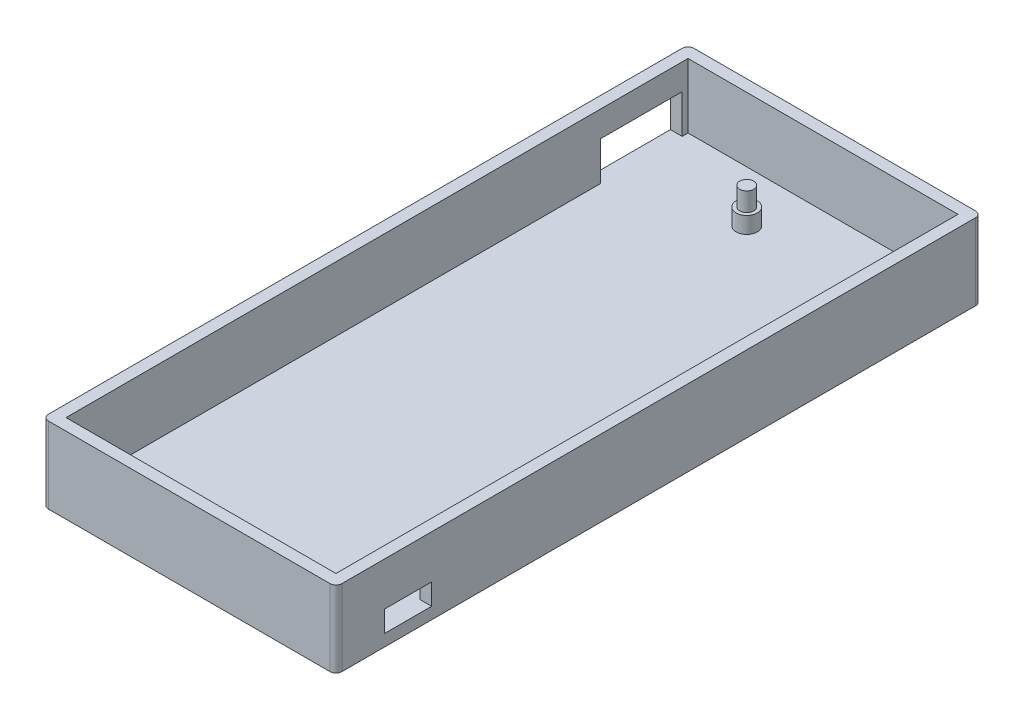
SolidWorks part; units mm, degrees
ref_plane "Front Plane" through (0, 0, 0) normal (0, 0, 1) x (1, 0, 0)
ref_plane "Top Plane" through (0, 0, 0) normal (0, 1, 0) x (1, 0, 0)
ref_plane "Right Plane" through (0, 0, 0) normal (1, 0, 0) x (0, 0, -1)
sketch "Sketch1" plane through (0, 0, 0) normal (0, 1, 0) x (1, 0, 0)
  line L1 (-77.0226, 53.0801) -> (-27.0226, 53.0801)
  line L2 (-77.0226, 53.0801) -> (-77.0226, -56.9199)
  line L3 (-77.0226, -56.9199) -> (-27.0226, -56.9199)
  line L4 (-27.0226, 53.0801) -> (-27.0226, -56.9199)
  dimension "D1" = 110
  dimension "D2" = 50
extrude "Boss-Extrude1" add sketch "Sketch1" along normal blind 2
sketch "Sketch2" plane through (0, 2, 0) normal (0, 1, 0) x (1, 0, 0)
  line L0 (-75.0226, 51.0801) -> (-75.0226, -54.9199)
  line L1 (-77.0226, 53.0801) -> (-27.0226, 53.0801)
  line L2 (-77.0226, 53.0801) -> (-77.0226, -56.9199)
  line L3 (-77.0226, -56.9199) -> (-27.0226, -56.9199)
  line L4 (-27.0226, 53.0801) -> (-27.0226, -56.9199)
  line L5 (-75.0226, -54.9199) -> (-29.0226, -54.9199)
  line L6 (-29.0226, 51.0801) -> (-29.0226, -54.9199)
  line L7 (-75.0226, 51.0801) -> (-29.0226, 51.0801)
  dimension "D1" = 2
extrude "Boss-Extrude3" add sketch "Sketch2" along normal blind 11
sketch "Sketch3" plane through (0, 2, 0) normal (0, 1, 0) x (1, 0, 0)
  circle A0 centre (-31.0226, 42.3801) radius 1.2
  circle A1 centre (-31.0226, -52.9199) radius 1.2
  circle A2 centre (-56.3226, 42.3801) radius 1.2
  circle A3 centre (-56.3226, -52.9199) radius 1.2
extrude "Boss-Extrude4" add sketch "Sketch3" along normal blind 11
sketch "Sketch4" plane through (0, 13, 0) normal (0, 1, 0) x (1, 0, 0)
  line L8 (-26.0226, 54.0801) -> (-78.0226, 54.0801)
  line L9 (-78.0226, 54.0801) -> (-78.0226, -57.9199)
  line L10 (-78.0226, -57.9199) -> (-26.0226, -57.9199)
  line L11 (-26.0226, -57.9199) -> (-26.0226, 54.0801)
  line L12 (-26.0226, 54.0801) -> (-78.0226, 54.0801)
  line L13 (-78.0226, 54.0801) -> (-78.0226, -57.9199)
  line L14 (-78.0226, -57.9199) -> (-26.0226, -57.9199)
  line L15 (-26.0226, -57.9199) -> (-26.0226, 54.0801)
  dimension "D1" = 3
extrude "Extrude-Thin1" add sketch "Sketch4" against normal blind 13 thin thin type one direction reverse wall 1
fillet "Fillet2" radius 2 4 edges at (-78.0226, 6.5, -54.0801) (-26.0226, 6.5, -54.0801) (-26.0226, 6.5, 57.9199) (-78.0226, 6.5, 57.9199)
sketch "Sketch5" plane through (0, 13, 0) normal (0, 1, 0) x (1, 0, 0)
  line L8 (-28.0226, 52.8801) -> (-76.0226, 52.8801)
  line L9 (-76.8226, 52.0801) -> (-76.8226, -55.9199)
  line L10 (-76.0226, -56.7199) -> (-28.0226, -56.7199)
  line L11 (-27.2226, -55.9199) -> (-27.2226, 52.0801)
  line L12 (-28.0226, 52.8801) -> (-76.0226, 52.8801)
  line L13 (-76.8226, 52.0801) -> (-76.8226, -55.9199)
  line L14 (-76.0226, -56.7199) -> (-28.0226, -56.7199)
  line L15 (-27.2226, -55.9199) -> (-27.2226, 52.0801)
  arc A8 (-76.0226, 52.8801) -> (-76.8226, 52.0801) centre (-76.0226, 52.0801) ccw
  arc A9 (-76.8226, -55.9199) -> (-76.0226, -56.7199) centre (-76.0226, -55.9199) ccw
  arc A10 (-28.0226, -56.7199) -> (-27.2226, -55.9199) centre (-28.0226, -55.9199) ccw
  arc A11 (-27.2226, 52.0801) -> (-28.0226, 52.8801) centre (-28.0226, 52.0801) ccw
  arc A12 (-76.0226, 52.8801) -> (-76.8226, 52.0801) centre (-76.0226, 52.0801) ccw
  arc A13 (-76.8226, -55.9199) -> (-76.0226, -56.7199) centre (-76.0226, -55.9199) ccw
  arc A14 (-28.0226, -56.7199) -> (-27.2226, -55.9199) centre (-28.0226, -55.9199) ccw
  arc A15 (-27.2226, 52.0801) -> (-28.0226, 52.8801) centre (-28.0226, 52.0801) ccw
  dimension "D1" = 1.2
extrude "Extrude-Thin3" add sketch "Sketch5" along normal blind 3 thin
sketch "Sketch6" plane through (0, 2, 0) normal (0, 1, 0) x (1, 0, 0)
  circle A0 centre (-56.3226, -52.9199) radius 1.8
  circle A1 centre (-31.0226, -52.9199) radius 1.8
  circle A2 centre (-56.3226, 42.3801) radius 1.8
  circle A3 centre (-31.0226, 42.3801) radius 1.8
extrude "Boss-Extrude5" add sketch "Sketch6" along normal blind 2.8
sketch "Sketch7" plane through (0, 2, 0) normal (0, 1, 0) x (1, 0, 0)
  line L0 (-31.0226, -52.9199) -> (-31.0226, -48.6199)
  line L1 (-31.0226, -48.6199) -> (-18.3371, -48.6199)
sketch "Sketch8" plane through (-26.0226, 0, 0) normal (1, 0, 0) x (0, 0, -1)
  line L0 (-52.9199, 2) -> (-48.6199, 2) construction
  line L2 (-48.6199, 2) -> (-40.6199, 2)
  line L3 (-48.6199, 2) -> (-48.6199, 5.6)
  line L4 (-48.6199, 5.6) -> (-40.6199, 5.6)
  line L5 (-40.6199, 2) -> (-40.6199, 5.6)
  dimension "D1" = 8
  dimension "D2" = 3.6
extrude "Cut-Extrude2" cut sketch "Sketch8" against normal blind 12.8
sketch "Sketch11" plane through (-78.0226, 0, 0) normal (-1, 0, 0) x (0, 0, 1)
  line L0 (-51.0801, 2) -> (54.9199, 2) construction
  line L1 (-50.0801, 7.8) -> (-36.9801, 7.8)
  line L2 (-50.0801, 7.8) -> (-50.0801, 2)
  line L3 (-50.0801, 2) -> (-36.9801, 2)
  line L4 (-36.9801, 7.8) -> (-36.9801, 2)
  line L5 (-51.0801, 13) -> (-51.0801, 2) construction
  dimension "D1" = 5.8
  dimension "D2" = 13.1
  dimension "D3" = 0
  dimension "D4" = 1
extrude "Cut-Extrude5" cut sketch "Sketch11" against normal blind 3
sketch "Sketch13" plane through (-76.8226, 0, 0) normal (1, 0, 0) x (0, 0, -1)
  line L1 (-55.9199, 13) -> (52.0801, 13)
  line L2 (-55.9199, 13) -> (-55.9199, 16)
  line L3 (-55.9199, 16) -> (52.0801, 16)
  line L4 (52.0801, 13) -> (52.0801, 16)
extrude "Cut-Extrude6" cut sketch "Sketch13" against normal blind 40 and the other way blind 70
sketch "Sketch14" plane through (0, 0, -52.8801) normal (0, 0, 1) x (1, 0, 0)
  line L1 (-76.0226, 13) -> (-28.0226, 13)
  line L2 (-76.0226, 13) -> (-76.0226, 16)
  line L3 (-76.0226, 16) -> (-28.0226, 16)
  line L4 (-28.0226, 13) -> (-28.0226, 16)
extrude "Cut-Extrude7" cut sketch "Sketch14" against normal blind 40 and the other way blind 160
sketch "Sketch15" plane through (0, 13, 0) normal (0, 1, 0) x (1, 0, 0)
  line L1 (-87.549, -61.3902) -> (-20.6815, -61.3902)
  line L2 (-87.549, -61.3902) -> (-87.549, 60.7623)
  line L3 (-87.549, 60.7623) -> (-20.6815, 60.7623)
  line L4 (-20.6815, -61.3902) -> (-20.6815, 60.7623)
extrude "Cut-Extrude8" cut sketch "Sketch15" along normal blind 40
sketch "Sketch16" plane through (0, 13, 0) normal (0, 1, 0) x (1, 0, 0)
  line L0 (-29.0226, -54.9199) -> (-29.0226, 51.0801) construction
  line L1 (-29.0226, 47.2331) -> (-66.4278, 47.2331)
  line L2 (-29.0226, 47.2331) -> (-29.0226, -54.9199)
  line L3 (-29.0226, -54.9199) -> (-66.4278, -54.9199)
  line L4 (-66.4278, 47.2331) -> (-66.4278, -54.9199)
  line L5 (-75.0226, -54.9199) -> (-29.0226, -54.9199) construction
extrude "Cut-Extrude9" cut sketch "Sketch16" against normal blind 5
sketch "Sketch17" plane through (0, 13, 0) normal (0, 1, 0) x (1, 0, 0)
  line L8 (-77.0226, 52.0801) -> (-77.0226, -55.9199)
  line L9 (-76.0226, -56.9199) -> (-28.0226, -56.9199)
  line L10 (-27.0226, -55.9199) -> (-27.0226, 52.0801)
  line L11 (-28.0226, 53.0801) -> (-76.0226, 53.0801)
  line L12 (-77.0226, 52.0801) -> (-77.0226, -55.9199)
  line L13 (-76.0226, -56.9199) -> (-28.0226, -56.9199)
  line L14 (-27.0226, -55.9199) -> (-27.0226, 52.0801)
  line L15 (-28.0226, 53.0801) -> (-76.0226, 53.0801)
  arc A8 (-77.0226, -55.9199) -> (-76.0226, -56.9199) centre (-76.0226, -55.9199) ccw
  arc A9 (-28.0226, -56.9199) -> (-27.0226, -55.9199) centre (-28.0226, -55.9199) ccw
  arc A10 (-27.0226, 52.0801) -> (-28.0226, 53.0801) centre (-28.0226, 52.0801) ccw
  arc A11 (-76.0226, 53.0801) -> (-77.0226, 52.0801) centre (-76.0226, 52.0801) ccw
  arc A12 (-77.0226, -55.9199) -> (-76.0226, -56.9199) centre (-76.0226, -55.9199) ccw
  arc A13 (-28.0226, -56.9199) -> (-27.0226, -55.9199) centre (-28.0226, -55.9199) ccw
  arc A14 (-27.0226, 52.0801) -> (-28.0226, 53.0801) centre (-28.0226, 52.0801) ccw
  arc A15 (-76.0226, 53.0801) -> (-77.0226, 52.0801) centre (-76.0226, 52.0801) ccw
  dimension "D1" = 1
extrude "Cut-Extrude-Thin2" cut sketch "Sketch17" against normal blind 55 thin
sketch "Sketch18" plane through (-77.0226, 0, 0) normal (-1, 0, 0) x (0, 0, 1)
  line L0 (-50.0801, 7.8) -> (-36.9801, 7.8) construction
  line L1 (-50.0801, 2) -> (-36.1801, 2)
  line L2 (-50.0801, 2) -> (-50.0801, 8.6)
  line L3 (-50.0801, 8.6) -> (-36.1801, 8.6)
  line L4 (-36.1801, 2) -> (-36.1801, 8.6)
  line L5 (-36.9801, 7.8) -> (-36.9801, 2) construction
  dimension "D1" = 0.8
  dimension "D2" = 0.8
extrude "Cut-Extrude10" cut sketch "Sketch18" against normal blind 2
